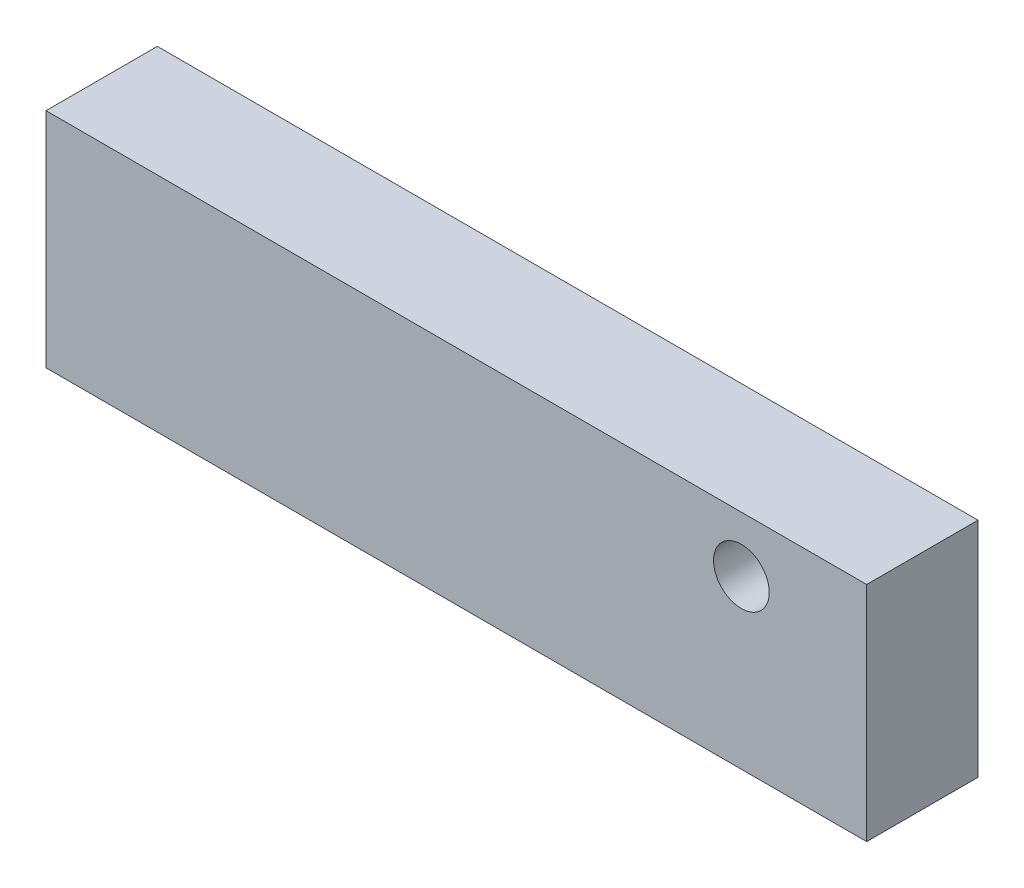
SolidWorks part; units mm, degrees
ref_plane "Front Plane" through (0, 0, 0) normal (0, 0, 1) x (1, 0, 0)
ref_plane "Top Plane" through (0, 0, 0) normal (0, 1, 0) x (1, 0, 0)
ref_plane "Right Plane" through (0, 0, 0) normal (1, 0, 0) x (0, 0, -1)
sketch "Sketch1" plane through (0, 0, 0) normal (0, 0, 1) x (1, 0, 0)
  line L1 (0, 0) -> (187.198, 0)
  line L2 (0, 0) -> (0, 50.8)
  line L3 (0, 50.8) -> (187.198, 50.8)
  line L4 (187.198, 0) -> (187.198, 50.8)
  dimension "D1" = 187.198
  dimension "D2" = 50.8
extrude "Boss-Extrude1" add sketch "Sketch1" along normal blind 25.4
sketch "Sketch3" plane through (0, 0, 25.4) normal (0, 0, 1) x (1, 0, 0)
  line L0 (187.198, 0) -> (187.198, 50.8) construction
  line L1 (187.198, 50.8) -> (0, 50.8) construction
  circle A0 centre (158.623, 38.1) radius 6.35
  dimension "D1" = 28.575
  dimension "D2" = 12.7
  dimension "D3" = 12.7
extrude "Cut-Extrude2" cut sketch "Sketch3" against normal blind 254
